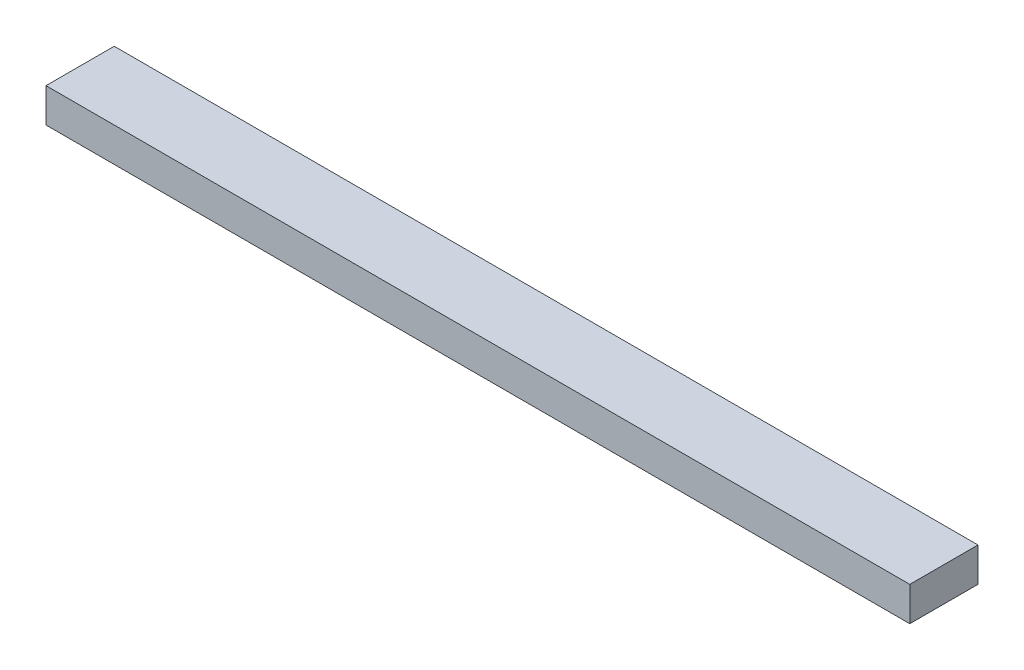
SolidWorks part; units mm, degrees
ref_plane "Front Plane" through (0, 0, 0) normal (0, 0, 1) x (1, 0, 0)
ref_plane "Top Plane" through (0, 0, 0) normal (0, 1, 0) x (1, 0, 0)
ref_plane "Right Plane" through (0, 0, 0) normal (1, 0, 0) x (0, 0, -1)
sketch "Sketch1" plane through (0, 0, 0) normal (0, 1, 0) x (1, 0, 0)
  line L1 (-80.391, -6.35) -> (80.391, -6.35)
  line L2 (-80.391, -6.35) -> (-80.391, 6.35)
  line L3 (-80.391, 6.35) -> (80.391, 6.35)
  line L4 (80.391, -6.35) -> (80.391, 6.35)
  line L5 (-80.391, -6.35) -> (80.391, 6.35) construction
  line L6 (-80.391, 6.35) -> (80.391, -6.35) construction
  point P0 (0, 0)
  dimension "D1" = 12.7
  dimension "D2" = 160.782
extrude "Boss-Extrude1" add sketch "Sketch1" along normal blind 6.35
